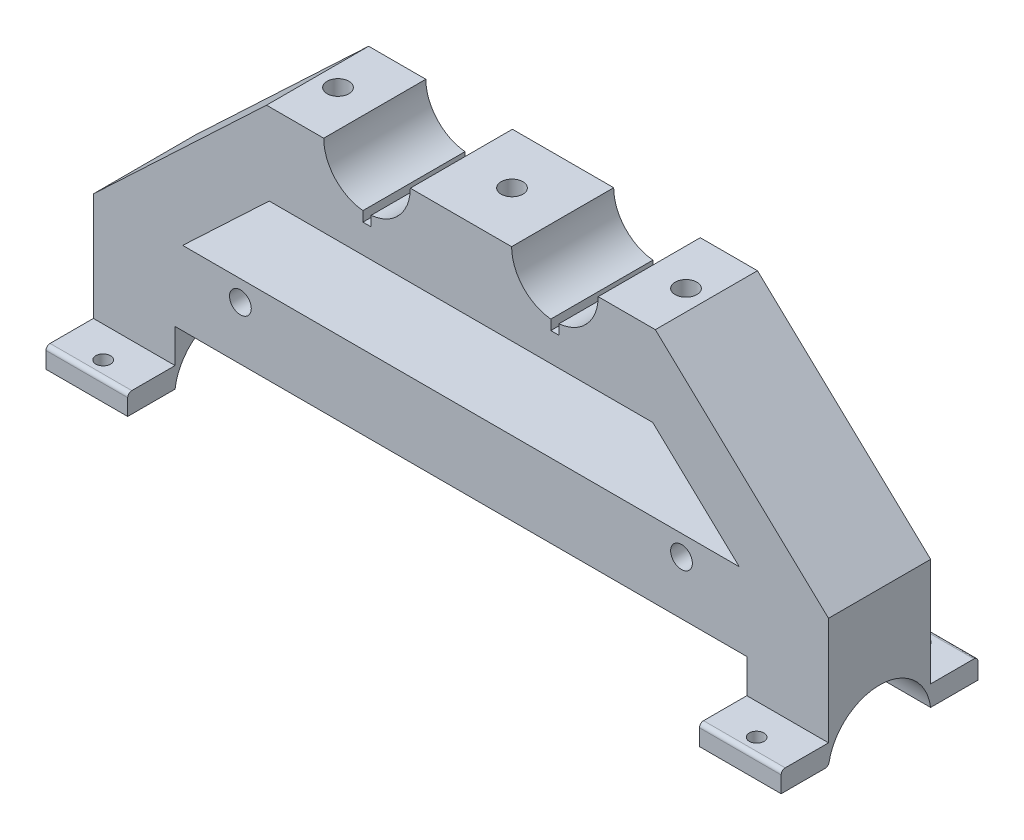
SolidWorks part; units mm, degrees
ref_plane "Front Plane" through (0, 0, 0) normal (0, 0, 1) x (1, 0, 0)
ref_plane "Top Plane" through (0, 0, 0) normal (0, 1, 0) x (1, 0, 0)
ref_plane "Right Plane" through (0, 0, 0) normal (1, 0, 0) x (0, 0, -1)
sketch "Sketch2" plane through (0, 0, 0) normal (0, 0, 1) x (1, 0, 0)
  line L0 (215.9, 0) -> (228.6, 0)
  line L4 (228.6, 0) -> (228.6, 101.6)
  line L9 (12.7, 0) -> (0, 0)
  line L10 (0, 0) -> (0, 101.6)
  line L12 (0, 101.6) -> (53.848, 152.4)
  line L13 (228.6, 101.6) -> (174.752, 152.4)
  line L14 (53.848, 152.4) -> (71.628, 152.4)
  line L15 (98.552, 152.4) -> (130.048, 152.4)
  line L19 (156.972, 152.4) -> (174.752, 152.4)
  line L20 (12.7, 0) -> (215.9, 0)
  arc A3 (71.628, 152.4) -> (98.552, 152.4) centre (85.09, 152.4) ccw
  arc A4 (130.048, 152.4) -> (156.972, 152.4) centre (143.51, 152.4) ccw
  dimension "D3" = 12.7
  dimension "D6" = 53.848
  dimension "D7" = 13.462
  dimension "D15" = 17.78
  dimension "D5" = 26.924
  dimension "D2" = 12.7
  dimension "D4" = 228.6
  dimension "D8" = 85.09
  dimension "D9" = 85.09
  dimension "D10" = 101.6
  dimension "D11" = 50.8
  dimension "D13" = 101.6
  dimension "D16" = 50.8
  dimension "D17" = 152.4
  dimension "D18" = 152.4
extrude "Boss-Extrude1" add sketch "Sketch2" along normal blind 50.8
sketch "Sketch7" plane through (0, 0, 50.8) normal (0, 0, 1) x (1, 0, 0)
  line L0 (228.6, 0) -> (228.6, 101.6) construction
  line L1 (0, 0) -> (228.6, 0)
  line L2 (0, 0) -> (0, 152.4)
  line L3 (0, 152.4) -> (228.6, 152.4)
  line L4 (228.6, 0) -> (228.6, 152.4)
  line L5 (130.048, 152.4) -> (98.552, 152.4) construction
extrude "Cut-Extrude5" cut sketch "Sketch7" against normal blind 19.05
sketch "Sketch9" plane through (0, 152.4, 0) normal (0, 1, 0) x (1, 0, 0)
  line L1 (71.628, 0) -> (53.848, 0) construction
  line L2 (130.048, 0) -> (98.552, 0) construction
  line L3 (114.3, 27.6941) -> (114.3, -48.8787) construction
  line L5 (174.752, -31.75) -> (174.752, 0) construction
  line L6 (53.848, -31.75) -> (53.848, 0) construction
  circle A0 centre (60.198, -15.875) radius 3.3782
  circle A1 centre (114.3, -15.875) radius 3.3782
  circle A2 centre (168.402, -15.875) radius 3.3782
  dimension "D1" = 6.7564
  dimension "D2" = 6.7564
  dimension "D3" = 6.35
  dimension "D4" = 15.875
  dimension "D5" = 15.875
  dimension "D6" = 60.452
extrude "Cut-Extrude7" cut sketch "Sketch9" against normal blind 27.94
sketch "Sketch10" plane through (0, 0, 31.75) normal (0, 0, 1) x (1, 0, 0)
  line L7 (27.7608, 101.6) -> (54.6848, 127)
  line L8 (54.6848, 127) -> (173.9152, 127)
  line L9 (27.7608, 101.6) -> (200.8392, 101.6)
  line L10 (0, 101.6) -> (53.848, 152.4) construction
  line L11 (173.9152, 127) -> (200.8392, 101.6)
  line L12 (174.752, 152.4) -> (228.6, 101.6) construction
  line L13 (98.552, 152.4) -> (130.048, 152.4) construction
  dimension "D1" = 25.4
  dimension "D2" = 19.05
  dimension "D3" = 19.05
  dimension "D4" = 25.4
extrude "Cut-Extrude8" cut sketch "Sketch10" against normal blind 40.64
sketch "Sketch12" plane through (0, 152.4, 0) normal (0, 1, 0) x (1, 0, 0)
  line L0 (85.09, -31.75) -> (85.09, 0)
  line L1 (71.628, -31.75) -> (98.552, -31.75) construction
  line L2 (98.552, 0) -> (71.628, 0) construction
  line L3 (85.09, 0) -> (86.36, 0)
  line L4 (86.36, 0) -> (86.36, -31.75)
  line L5 (86.36, -31.75) -> (83.82, -31.75)
  line L6 (83.82, -31.75) -> (83.82, 0)
  line L7 (83.82, 0) -> (85.09, 0)
  line L8 (114.3, 104.6898) -> (114.3, -104.6898) construction
  line L9 (130.048, 0) -> (98.552, 0) construction
  line L10 (144.78, 0) -> (143.51, 0)
  line L11 (144.78, -31.75) -> (144.78, 0)
  line L12 (142.24, -31.75) -> (144.78, -31.75)
  line L13 (142.24, 0) -> (142.24, -31.75)
  line L14 (143.51, 0) -> (142.24, 0)
  line L15 (143.51, -31.75) -> (143.51, 0)
  point P14 (114.3, 0)
  dimension "D1" = 1.27
  dimension "D2" = 1.27
extrude "Cut-Extrude9" cut sketch "Sketch12" against normal blind 16.51 contours L5 L4 L3 L0 | L7 L6 L5 L0 | L14 L13 L12 L11 L10
sketch "Sketch13" plane through (0, 0, 31.75) normal (0, 0, 1) x (1, 0, 0)
  line L0 (228.6, 0) -> (228.6, 101.6) construction
  line L1 (27.7608, 101.6) -> (200.8392, 101.6) construction
  line L2 (0, 0) -> (0, 101.6) construction
  circle A0 centre (45.72, 95.25) radius 3.3782
  circle A1 centre (182.88, 95.25) radius 3.3782
  dimension "D1" = 6.7564
  dimension "D2" = 6.7564
  dimension "D3" = 6.35
  dimension "D4" = 6.35
  dimension "D5" = 45.72
  dimension "1.8" = 45.72
extrude "Cut-Extrude10" cut sketch "Sketch13" against normal up to next
sketch "Sketch14" plane through (0, 0, 0) normal (0, 0, -1) x (-1, 0, 0)
  line L0 (-185.674, 95.25) -> (49814.326, 95.25) construction
  line L1 (-182.88, 95.25) -> (-182.88, -49904.75) construction
  line L2 (-182.88, 95.25) -> (-182.88, 59.69)
  line L3 (-188.6748, 59.69) -> (-50188.6748, 59.69) construction
  line L5 (-228.6, 0) -> (-228.6, 101.6) construction
  line L6 (-228.6, 59.69) -> (0, 59.69)
  line L7 (-228.6, 59.69) -> (-228.6, 0)
  line L8 (-228.6, 0) -> (0, 0)
  line L9 (0, 59.69) -> (0, 0)
  line M20 (-228.6, 101.6) -> (-228.6, 0)
  line M21 (-228.6, 0) -> (0, 0)
  line M22 (0, 0) -> (0, 101.6)
  dimension "D1" = 35.56
extrude "Cut-Extrude11" cut sketch "Sketch14" against normal through all contours L6 M20 M21 M22
sketch "Sketch15" plane through (228.6, 0, 0) normal (1, 0, 0) x (0, 0, -1)
  line L0 (-31.75, 59.69) -> (0, 59.69) construction
  circle A0 centre (-15.875, 59.69) radius 16.002
  dimension "D1" = 32.004
extrude "Cut-Extrude12" cut sketch "Sketch15" against normal through all
sketch "Sketch16" plane through (0, 0, 31.75) normal (0, 0, 1) x (1, 0, 0)
  line L2 (228.6, 61.7021) -> (203.2, 61.7021)
  line L3 (0, 61.7021) -> (25.4, 61.7021)
  line L4 (0, 61.7021) -> (0, 68.0521)
  line L5 (0, 68.0521) -> (25.4, 68.0521)
  line L6 (25.4, 61.7021) -> (25.4, 68.0521)
  line L7 (228.6, 61.7021) -> (228.6, 68.0521)
  line L8 (228.6, 68.0521) -> (203.2, 68.0521)
  line L9 (203.2, 61.7021) -> (203.2, 68.0521)
  dimension "D1" = 25.4
  dimension "D2" = 25.4
  dimension "D3" = 6.35
  dimension "D4" = 6.35
extrude "Boss-Extrude2" add sketch "Sketch16" along normal blind 14.732
sketch "Sketch17" plane through (0, 0, 0) normal (0, 0, -1) x (-1, 0, 0)
  line L0 (-228.6, 61.7021) -> (-203.2, 61.7021)
  line L1 (-228.6, 61.7021) -> (-228.6, 68.0521)
  line L2 (-228.6, 68.0521) -> (-203.2, 68.0521)
  line L3 (-203.2, 61.7021) -> (-203.2, 68.0521)
  line L4 (-25.4, 61.7021) -> (0, 61.7021)
  line L5 (-25.4, 61.7021) -> (-25.4, 68.0521)
  line L6 (-25.4, 68.0521) -> (0, 68.0521)
  line L7 (0, 61.7021) -> (0, 68.0521)
  dimension "D1" = 25.4
  dimension "D2" = 6.35
  dimension "D3" = 25.4
  dimension "D4" = 6.35
extrude "Boss-Extrude3" add sketch "Sketch17" along normal blind 14.732
fillet "Fillet7" radius 1.27 1 edges at (215.9, 68.0521, 46.482)
fillet "Fillet8" radius 1.27 1 edges at (215.9, 68.0521, -14.732)
fillet "Fillet9" radius 1.27 1 edges at (12.7, 68.0521, -14.732)
fillet "Fillet10" radius 1.27 1 edges at (12.7, 68.0521, 46.482)
sketch "Sketch20" plane through (0, 0, 31.75) normal (0, 0, 1) x (1, 0, 0)
  line L0 (114.3, 61.7021) -> (114.3, 50061.7021) construction
  line L1 (25.4, 61.7021) -> (25.4, 68.0521) construction
  line L2 (25.4, 61.7021) -> (203.2, 61.7021) construction
  line L3 (48.768, 95.25) -> (50048.768, 95.25) construction
  line L4 (45.72, 95.25) -> (45.72, -49904.75) construction
  line L5 (66.04, 61.7021) -> (25.4, 61.7021)
  line L6 (25.4, 61.7021) -> (25.4, 78.5903)
  line L7 (25.4, 78.5903) -> (203.2, 78.5903)
  line L8 (66.04, 61.7021) -> (162.56, 61.7021)
  line L9 (203.2, 61.7021) -> (203.2, 78.5903)
  line L10 (162.56, 61.7021) -> (203.2, 61.7021)
  point P4 (114.3, 61.7021)
  point P13 (114.3, 78.5903)
  point P15 (182.88, 61.7021)
  point P18 (114.3, 61.7021)
  point P20 (45.72, 61.7021)
extrude "Cut-Extrude14" cut sketch "Sketch20" against normal through all
fillet "Fillet15" radius 1.27 1 edges at (215.9, 61.7021, 31.75)
sketch "Sketch22" plane through (0, 61.7021, 0) normal (0, -1, 0) x (1, 0, 0)
  line L0 (0, 31.75) -> (25.4, 31.75) construction
  line L4 (25.4, 15.875) -> (-49974.6, 15.875) construction
  line L5 (203.2, 31.75) -> (25.4, 31.75) construction
  line L7 (0, 31.75) -> (0, 0) construction
  line L8 (114.3, 31.75) -> (114.3, -49968.25) construction
  line L9 (203.2, 0) -> (25.4, 0) construction
  circle A0 centre (12.7, 41.402) radius 2.286
  circle A1 centre (12.7, -9.652) radius 2.286
  circle A2 centre (215.9, -9.652) radius 2.286
  circle A3 centre (215.9, 41.402) radius 2.286
  point P14 (114.3, 31.75)
  point P20 (0, 15.875)
  point P25 (114.3, 0)
  dimension "D1" = 9.652
  dimension "D2" = 4.572
extrude "Cut-Extrude15" cut sketch "Sketch22" against normal through all
